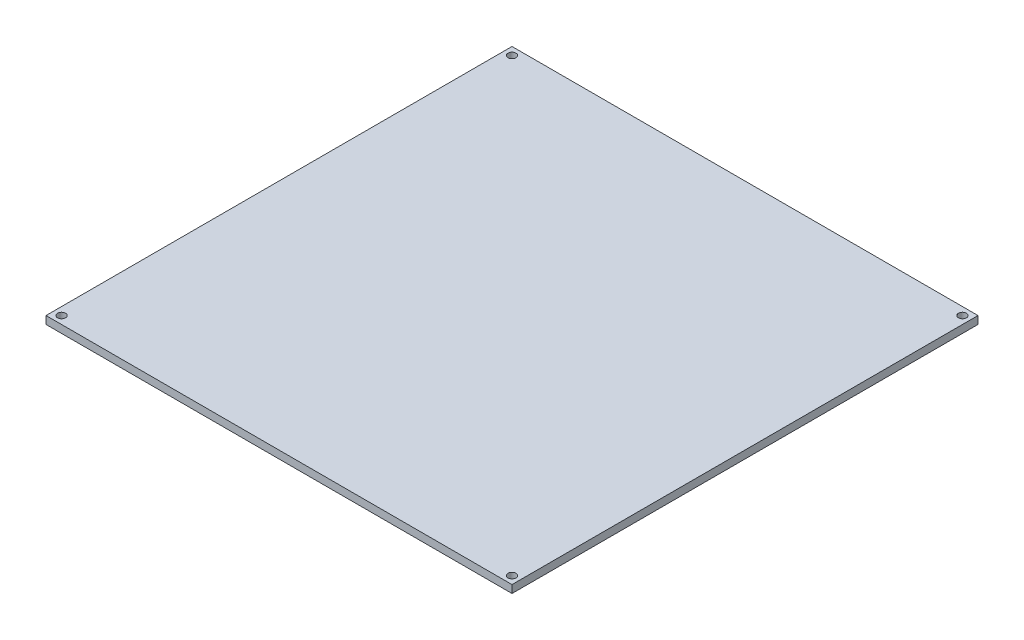
SolidWorks part; units mm, degrees
ref_plane "前视基准面" through (0, 0, 0) normal (0, 0, 1) x (1, 0, 0)
ref_plane "上视基准面" through (0, 0, 0) normal (0, 1, 0) x (1, 0, 0)
ref_plane "右视基准面" through (0, 0, 0) normal (1, 0, 0) x (0, 0, -1)
sketch "草图3" plane through (0, 0, 0) normal (0, 1, 0) x (1, 0, 0)
  line L0 (0, 3) -> (0, 15)
  line L1 (3, 0) -> (207, 0)
  line L2 (0, 3) -> (0, 207)
  line L3 (3, 210) -> (207, 210)
  line L4 (210, 3) -> (210, 207)
  line L5 (0, 15) -> (15, 15) construction
  line L6 (15, 15) -> (15, 0) construction
  line L7 (207, 210) -> (195, 210)
  line L8 (195, 210) -> (195, 195) construction
  line L9 (195, 195) -> (198.1, 195) construction
  line L11 (195, 195) -> (15, 195)
  line L12 (195, 195) -> (195, 15)
  line L13 (195, 15) -> (15, 15)
  line L14 (15, 195) -> (15, 15)
  line L15 (0, 195) -> (15, 195) construction
  line L16 (0, 195) -> (0, 207)
  line L17 (3, 210) -> (15, 210)
  line L18 (15, 195) -> (15, 210) construction
  line L19 (195, 15) -> (198.1, 15) construction
  line L20 (195, 15) -> (195, 0) construction
  line L21 (195, 0) -> (207, 0)
  line L22 (210, 15) -> (210, 3)
  line L23 (11.9, 175) -> (11.9, 35)
  line L26 (35, 11.9) -> (175, 11.9)
  line L27 (175, 11.9) -> (185, 11.9) construction
  line L29 (198.1, 35) -> (198.1, 175)
  line L30 (195, 15) -> (190, 15)
  line L31 (15, 195) -> (35, 195)
  line L32 (175, 198.1) -> (35, 198.1)
  line L33 (195, 195) -> (195, 175)
  line L35 (3, 0) -> (3, 3) construction
  line L37 (3, 210) -> (3, 207) construction
  line L39 (207, 210) -> (207, 207) construction
  line L41 (207, 0) -> (207, 3) construction
  line L42 (15, 195) -> (18, 195)
  line L43 (18, 195) -> (18, 192) construction
  line L44 (195, 195) -> (192, 195)
  line L45 (192, 195) -> (192, 192) construction
  line L46 (195, 15) -> (192, 15)
  line L47 (192, 15) -> (192, 18) construction
  line L48 (15, 15) -> (18, 15)
  line L49 (18, 15) -> (18, 18) construction
  line L50 (195, 195) -> (175, 195)
  line L51 (35, 198.1) -> (20, 198.1)
  line L52 (3, 3) -> (0, 3) construction
  line L53 (175, 198.1) -> (190, 198.1)
  line L54 (195, 15) -> (195, 35)
  line L55 (195, 195) -> (195, 190)
  line L56 (195, 15) -> (175, 15)
  line L57 (195, 15) -> (195, 20)
  line L58 (15, 15) -> (15, 35)
  line L59 (15, 15) -> (20, 15)
  line L60 (15, 195) -> (15, 175)
  line L61 (15, 15) -> (15, 20)
  line L69 (25, 11.9) -> (35, 11.9) construction
  line L70 (11.9, 35) -> (11.9, 25) construction
  line L71 (198.1, 35) -> (198.1, 15) construction
  line L75 (201.2, 15) -> (210, 15) construction
  line L77 (201.2, 15) -> (198.1, 15) construction
  line L81 (198.1, 175) -> (198.1, 195) construction
  line L86 (175, 198.1) -> (195, 198.1) construction
  line L91 (35, 198.1) -> (15, 198.1) construction
  line L96 (11.9, 175) -> (11.9, 195) construction
  line L101 (15, 195) -> (15, 190)
  line L102 (15, 190) -> (11.9, 190)
  line L103 (11.9, 190) -> (11.9, 175)
  line L104 (15, 20) -> (11.9, 20)
  line L105 (11.9, 20) -> (11.9, 35)
  line L106 (20, 15) -> (20, 11.9)
  line L107 (20, 11.9) -> (35, 11.9)
  line L108 (190, 15) -> (190, 11.9)
  line L109 (190, 11.9) -> (175, 11.9)
  line L110 (195, 20) -> (198.1, 20)
  line L111 (198.1, 20) -> (198.1, 35)
  line L112 (195, 190) -> (198.1, 190)
  line L113 (198.1, 190) -> (198.1, 175)
  line L114 (190, 198.1) -> (190, 195)
  line L115 (20, 198.1) -> (20, 195)
  line L116 (3, 207) -> (0, 207) construction
  line L117 (207, 207) -> (210, 207) construction
  line L118 (207, 3) -> (210, 3) construction
  circle A0 centre (3, 3) radius 1.55
  circle A1 centre (3, 207) radius 1.55
  circle A2 centre (207, 207) radius 1.55
  circle A3 centre (207, 3) radius 1.55
  circle A4 centre (18, 192) radius 1.55
  circle A5 centre (192, 192) radius 1.55
  circle A6 centre (192, 18) radius 1.55
  circle A7 centre (18, 18) radius 1.55
  arc A8 (0, 207) -> (3, 210) centre (3, 207) cw
  arc A9 (207, 210) -> (210, 207) centre (207, 207) cw
  arc A10 (210, 3) -> (207, 0) centre (207, 3) cw
  arc A11 (3, 0) -> (0, 3) centre (3, 3) cw
extrude "凸台-拉伸2" add sketch "草图3" along normal blind 3 contours L11 L50 L31 L14 L60 L58 L13 L30 L54 L12 L33 A7 A6 A5 A4
